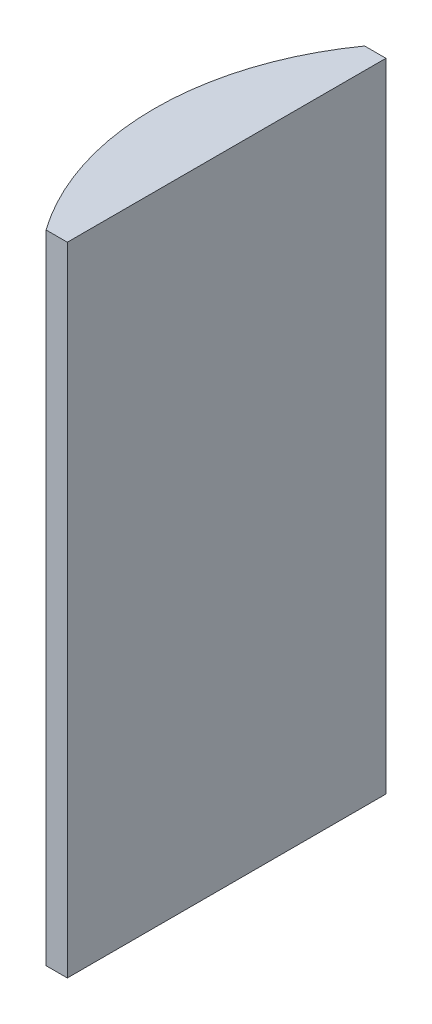
SolidWorks part; units mm, degrees
ref_plane "前视基准面" through (0, 0, 0) normal (0, 0, 1) x (1, 0, 0)
ref_plane "上视基准面" through (0, 0, 0) normal (0, 1, 0) x (1, 0, 0)
ref_plane "右视基准面" through (0, 0, 0) normal (1, 0, 0) x (0, 0, -1)
sketch "草图1" plane through (0, 0, 0) normal (0, 1, 0) x (1, 0, 0)
  line L0 (10.7432, 0) -> (-607.0701, 0) construction
  line L1 (-16.6976, 15) -> (-14.6948, 15)
  line L2 (-16.6976, -15) -> (-14.6948, -15)
  line L3 (-14.6948, 15) -> (-14.6948, -15)
  arc A0 (-16.6976, 15) -> (-16.6976, -15) centre (4.3552, 0) ccw
  point P19 (-21.4948, 0)
  point P20 (-14.6948, 0)
  dimension "D2" = 15
  dimension "D3" = 25.85
  dimension "D4" = 6.8
  dimension "D1" = 15
extrude "凸台-拉伸1" add sketch "草图1" along normal blind 60
